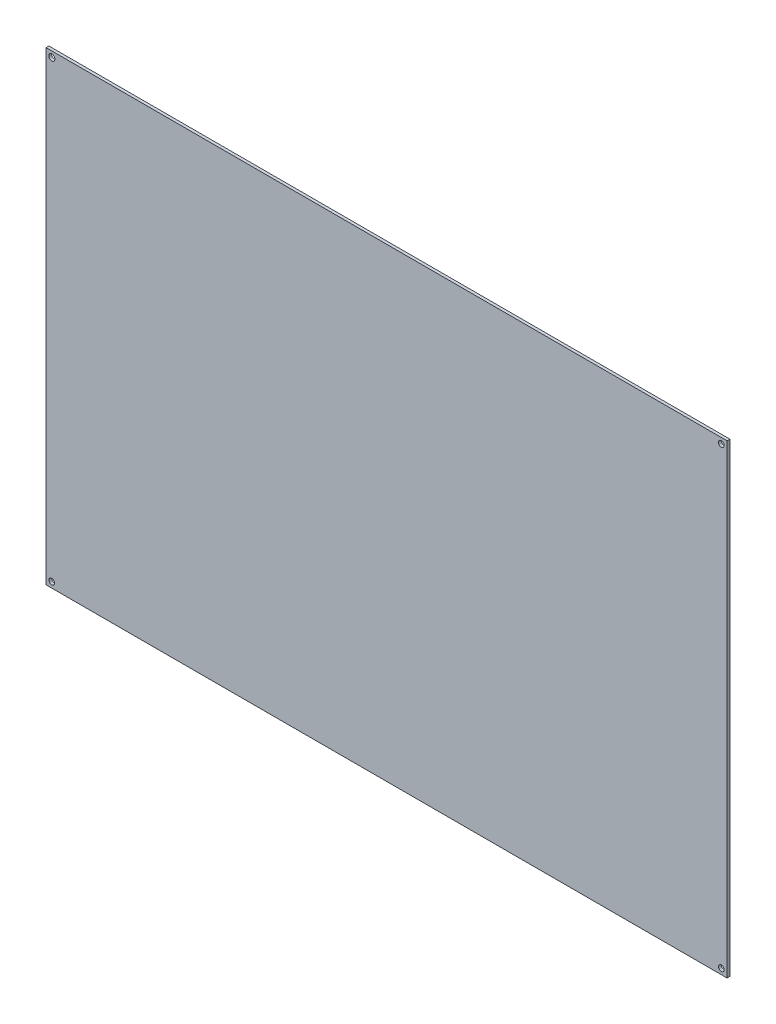
SolidWorks part; units mm, degrees
material "PC High Viscosity"
ref_plane "Front Plane" through (0, 0, 0) normal (0, 0, 1) x (1, 0, 0)
ref_plane "Top Plane" through (0, 0, 0) normal (0, 1, 0) x (1, 0, 0)
ref_plane "Right Plane" through (0, 0, 0) normal (1, 0, 0) x (0, 0, -1)
sketch "Sketch1" plane through (0, 0, 0) normal (0, 0, 1) x (1, 0, 0)
  line L1 (381, -260.35) -> (-381, -260.35)
  line L2 (381, -260.35) -> (381, 260.35)
  line L3 (381, 260.35) -> (-381, 260.35)
  line L4 (-381, -260.35) -> (-381, 260.35)
  line L5 (381, -260.35) -> (-381, 260.35) construction
  line L6 (381, 260.35) -> (-381, -260.35) construction
  point P0 (0, 0)
  dimension "D1" = 520.7
  dimension "D2" = 762
extrude "Boss-Extrude1" add sketch "Sketch1" along normal blind 3.175
sketch "Sketch2" plane through (0, 0, 3.175) normal (0, 0, 1) x (1, 0, 0)
  line L0 (381, 260.35) -> (-381, 260.35) construction
  line L1 (-381, 260.35) -> (-381, -260.35) construction
  line L2 (381, -260.35) -> (381, 260.35) construction
  line L3 (-381, -260.35) -> (381, -260.35) construction
  circle A0 centre (-374.65, 254) radius 3.429
  circle A1 centre (374.65, 254) radius 3.175
  circle A2 centre (-374.65, -254) radius 3.175
  circle A3 centre (374.65, -254) radius 3.175
  dimension "D2" = 6.858
  dimension "D5" = 6.35
  dimension "D8" = 6.35
  dimension "D11" = 6.35
  dimension "D1" = 6.35
  dimension "D3" = 6.35
  dimension "D4" = 6.35
  dimension "D6" = 6.35
  dimension "D7" = 6.35
  dimension "D9" = 6.35
  dimension "D10" = 6.35
extrude "Cut-Extrude1" cut sketch "Sketch2" against normal blind 6.35
